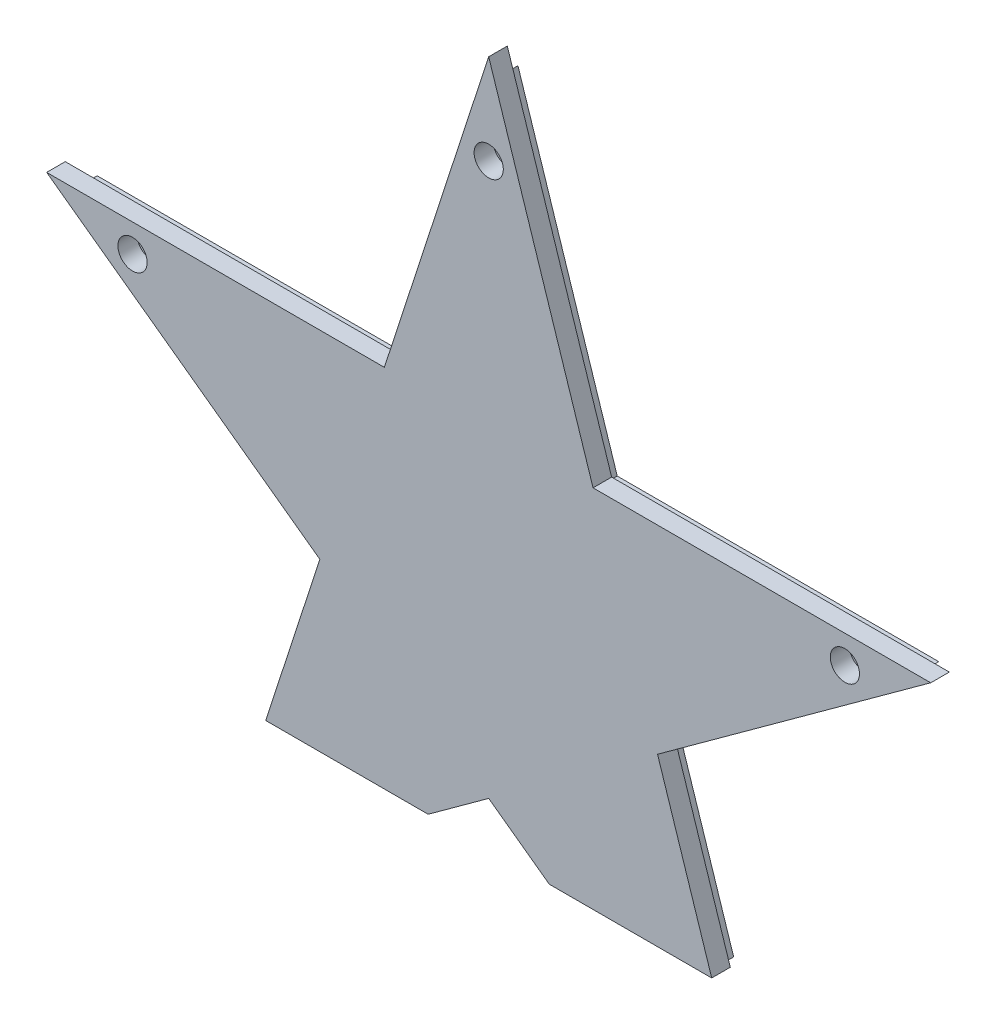
SolidWorks part; units mm, degrees
ref_plane "Alzado" through (0, 0, 0) normal (0, 0, 1) x (1, 0, 0)
ref_plane "Planta" through (0, 0, 0) normal (0, 1, 0) x (1, 0, 0)
ref_plane "Vista lateral" through (0, 0, 0) normal (1, 0, 0) x (0, 0, -1)
sketch "Croquis1" plane through (0, 0, 0) normal (0, 0, 1) x (1, 0, 0)
  line L0 (79.2165, 25.739) -> (18.7005, 25.739)
  line L1 (18.7005, 25.739) -> (0, 83.2931)
  line L2 (0, 83.2931) -> (-18.7005, 25.739)
  line L3 (-18.7005, 25.739) -> (-79.2165, 25.739)
  line L4 (-79.2165, 25.739) -> (-30.258, -9.8314)
  line L5 (-30.258, -9.8314) -> (-40.615, -41.707)
  line L6 (-13.615, -41.707) -> (0, -31.8151)
  line L7 (0, -31.8151) -> (13.615, -41.707)
  line L8 (40.615, -41.707) -> (30.258, -9.8314)
  line L9 (30.258, -9.8314) -> (79.2165, 25.739)
  line L10 (80.1398, 26.039) -> (18.9184, 26.039)
  line L11 (18.9184, 26.039) -> (0, 84.2639)
  line L12 (0, 84.2639) -> (-18.9184, 26.039)
  line L13 (-18.9184, 26.039) -> (-80.1398, 26.039)
  line L14 (-80.1398, 26.039) -> (-30.6107, -9.946)
  line L15 (-30.6107, -9.946) -> (-49.5291, -68.171)
  line L16 (-49.5291, -68.171) -> (0, -32.186)
  line L17 (0, -32.186) -> (49.5291, -68.171)
  line L18 (49.5291, -68.171) -> (30.6107, -9.946)
  line L19 (30.6107, -9.946) -> (80.1398, 26.039)
  line L20 (80.1398, 26.039) -> (18.9184, 26.039) construction
  line L21 (18.9184, 26.039) -> (0, 84.2639) construction
  line L22 (0, 84.2639) -> (-18.9184, 26.039) construction
  line L23 (-18.9184, 26.039) -> (-80.1398, 26.039) construction
  line L24 (-80.1398, 26.039) -> (-30.6107, -9.946) construction
  line L27 (0, -32.186) -> (49.5291, -68.171) construction
  line L28 (49.5291, -68.171) -> (30.6107, -9.946) construction
  line L29 (30.6107, -9.946) -> (80.1398, 26.039) construction
  line L30 (-30.258, -9.8314) -> (-48.9585, -67.3855) construction
  line L31 (-48.9585, -67.3855) -> (0, -31.8151) construction
  line L32 (-40.615, -41.707) -> (-13.615, -41.707)
  line L33 (-13.615, -41.707) -> (13.615, -41.707) construction
  line L34 (13.615, -41.707) -> (40.615, -41.707)
  line L35 (48.9585, -67.3855) -> (30.258, -9.8314) construction
  line L36 (0, -31.8151) -> (48.9585, -67.3855) construction
  line L42 (-30.6107, -9.946) -> (-49.5291, -68.171) construction
  line L43 (-49.5291, -68.171) -> (0, -32.186) construction
  dimension "D3" = 27
  dimension "D1" = 0
  dimension "D2" = 0.3
extrude "Saliente-Extruir1" add sketch "Croquis1" along normal blind 2
sketch "Croquis3" plane through (0, 0, 2) normal (0, 0, 1) x (1, 0, 0)
  line L0 (-41.9819, -41.707) -> (-11.4033, -41.707)
  line L1 (-51.4312, -70.789) -> (0, -33.422) construction
  line L2 (-11.4033, -41.707) -> (0, -33.422)
  line L3 (0, -33.422) -> (11.4033, -41.707)
  line L4 (0, -33.422) -> (51.4312, -70.789) construction
  line L5 (11.4033, -41.707) -> (41.9819, -41.707)
  line L12 (30.258, -9.8314) -> (79.2165, 25.739)
  line L13 (79.2165, 25.739) -> (18.7005, 25.739)
  line L14 (18.7005, 25.739) -> (0, 83.2931)
  line L15 (0, 83.2931) -> (-18.7005, 25.739)
  line L16 (-18.7005, 25.739) -> (-79.2165, 25.739)
  line L17 (-79.2165, 25.739) -> (-30.258, -9.8314)
  line L18 (-30.258, -9.8314) -> (-40.615, -41.707)
  line L19 (-40.615, -41.707) -> (-13.615, -41.707)
  line L20 (-13.615, -41.707) -> (0, -31.8151)
  line L21 (0, -31.8151) -> (13.615, -41.707)
  line L22 (13.615, -41.707) -> (40.615, -41.707)
  line L23 (40.615, -41.707) -> (30.258, -9.8314)
  line L24 (30.258, -9.8314) -> (79.2165, 25.739) construction
  line L25 (79.2165, 25.739) -> (18.7005, 25.739) construction
  line L26 (18.7005, 25.739) -> (0, 83.2931) construction
  line L27 (0, 83.2931) -> (-18.7005, 25.739) construction
  line L28 (-18.7005, 25.739) -> (-79.2165, 25.739) construction
  line L29 (-79.2165, 25.739) -> (-30.258, -9.8314) construction
  line L30 (-30.258, -9.8314) -> (-40.615, -41.707) construction
  line L31 (-40.615, -41.707) -> (-13.615, -41.707) construction
  line L32 (-13.615, -41.707) -> (0, -31.8151) construction
  line L33 (0, -31.8151) -> (13.615, -41.707) construction
  line L34 (13.615, -41.707) -> (40.615, -41.707) construction
  line L35 (40.615, -41.707) -> (30.258, -9.8314) construction
  line L46 (19.645, 27.039) -> (0, 87.5)
  line L47 (83.2174, 27.039) -> (19.645, 27.039)
  line L48 (31.7862, -10.328) -> (83.2174, 27.039)
  line L49 (51.4312, -70.789) -> (31.7862, -10.328)
  line L50 (0, -33.422) -> (51.4312, -70.789)
  line L51 (-51.4312, -70.789) -> (0, -33.422)
  line L52 (-31.7862, -10.328) -> (-51.4312, -70.789)
  line L53 (-83.2174, 27.039) -> (-31.7862, -10.328)
  line L54 (-19.645, 27.039) -> (-83.2174, 27.039)
  line L55 (0, 87.5) -> (-19.645, 27.039)
  line L56 (19.645, 27.039) -> (0, 87.5)
  line L57 (83.2174, 27.039) -> (19.645, 27.039)
  line L58 (31.7862, -10.328) -> (83.2174, 27.039)
  line L59 (41.9819, -41.707) -> (31.7862, -10.328)
  line L62 (-31.7862, -10.328) -> (-41.9819, -41.707)
  line L63 (-83.2174, 27.039) -> (-31.7862, -10.328)
  line L64 (-19.645, 27.039) -> (-83.2174, 27.039)
  line L65 (0, 87.5) -> (-19.645, 27.039)
  dimension "D1" = 0
  dimension "D2" = 0
extrude "Saliente-Extruir2" add sketch "Croquis3" along normal blind 3.5
sketch "Croquis2" plane through (0, 0, 5.5) normal (0, 0, 1) x (1, 0, 0)
  circle A0 centre (41.4389, -57.0357) radius 1.25 construction
  circle A1 centre (-67.0495, 21.7857) radius 1.25 construction
  circle A2 centre (67.0495, 21.7857) radius 1.25 construction
  circle A3 centre (0, 70.5) radius 1.25 construction
  circle A4 centre (41.4389, -57.0357) radius 1.25 construction
  circle A5 centre (-67.0495, 21.7857) radius 1.25 construction
  circle A6 centre (67.0495, 21.7857) radius 1.25 construction
  circle A7 centre (0, 70.5) radius 1.25 construction
  circle A8 centre (0, 70.5) radius 1.85
  circle A9 centre (67.0495, 21.7857) radius 1.85
  circle A11 centre (-67.0495, 21.7857) radius 1.85
  dimension "D1" = 0.6
extrude "Cortar-Extruir4" cut sketch "Croquis2" against normal blind 10
sketch "Croquis4" plane through (0, 0, 5.5) normal (0, 0, 1) x (1, 0, 0)
  circle A0 centre (67.0495, 21.7857) radius 2.75
  circle A1 centre (0, 70.5) radius 2.75
  circle A2 centre (-67.0495, 21.7857) radius 2.75
  dimension "D1" = 5.5
extrude "Cortar-Extruir5" cut sketch "Croquis4" against normal blind 3.6
